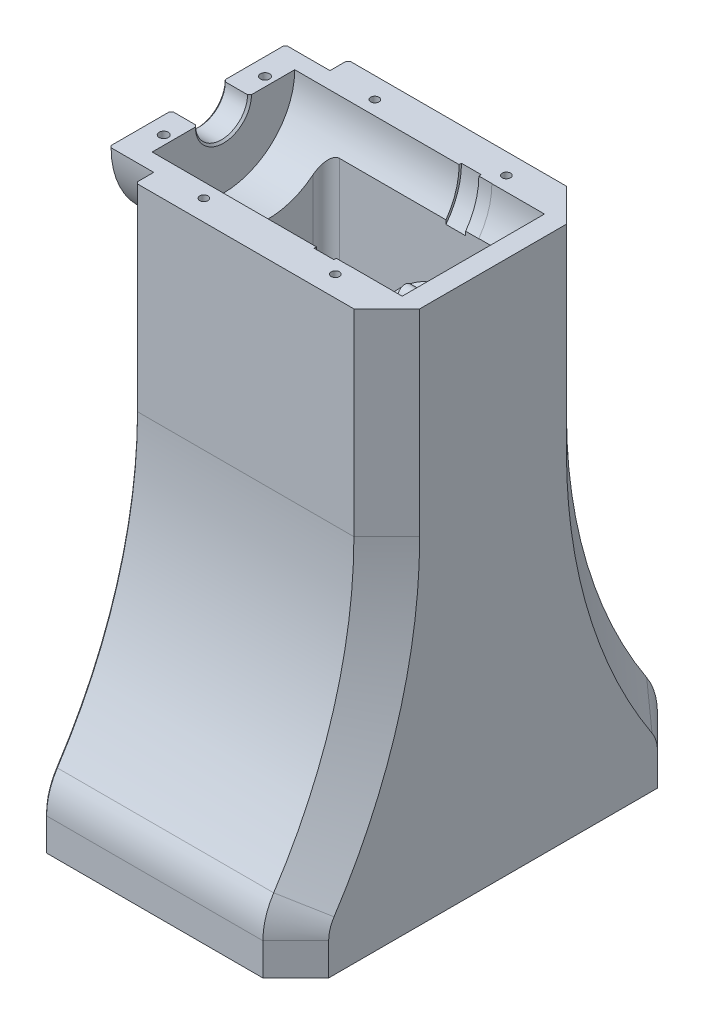
SolidWorks part; units mm, degrees
ref_plane "Front Plane" through (0, 0, 0) normal (0, 0, 1) x (1, 0, 0)
ref_plane "Top Plane" through (0, 0, 0) normal (0, 1, 0) x (1, 0, 0)
ref_plane "Right Plane" through (0, 0, 0) normal (1, 0, 0) x (0, 0, -1)
sketch "Sketch1" plane through (0, 0, 0) normal (0, 0, 1) x (1, 0, 0)
  line L1 (0, 0) -> (0, 5.0292)
  line L2 (0, 5.0292) -> (5.0546, 5.0292)
  line L3 (5.0546, 5.0292) -> (5.0546, 13.7668)
  line L4 (5.0546, 13.7668) -> (36.8046, 13.7668)
  line L5 (43.1546, 13.7668) -> (43.1546, 13.7414)
  line L6 (53.3146, 0) -> (0, 0)
  line L8 (43.1546, 13.7414) -> (53.3146, 13.7414)
  line L9 (53.3146, 13.7414) -> (53.3146, 0)
  line L10 (36.8046, 13.7668) -> (36.8046, 14.224)
  line L11 (36.8046, 14.224) -> (40.6146, 14.224)
  line L12 (40.6146, 14.224) -> (40.6146, 13.7668)
  line L13 (40.6146, 13.7668) -> (43.1546, 13.7668)
  point P8 (38.7096, 14.224)
  dimension "D1" = 5.0546
  dimension "D2" = 31.75
  dimension "D3" = 5.0292
  dimension "D4" = 38.1
  dimension "D5" = 13.7668
  dimension "D6" = 0.0254
  dimension "D7" = 10.16
  dimension "D8" = 35.56
  dimension "D9" = 14.224
revolve "REVOLVE MOTOR" add sketch "Sketch1" angle 360 about L6
sketch "Sketch2" plane through (5.0546, 0, 0) normal (-1, 0, 0) x (0, 0, 1)
  line L0 (0, -14.6304) -> (0, -12.9032) construction
  line L1 (-1.4224, -14.6304) -> (-1.4224, -12.9032)
  line L2 (1.4224, -14.6304) -> (1.4224, -12.9032)
  line L3 (0, 14.6304) -> (0, 12.9032) construction
  line L4 (1.4224, 14.6304) -> (1.4224, 12.9032)
  line L5 (-1.4224, 14.6304) -> (-1.4224, 12.9032)
  arc A0 (-1.4224, -14.6304) -> (1.4224, -14.6304) centre (0, -14.6304) ccw
  arc A1 (1.4224, -12.9032) -> (-1.4224, -12.9032) centre (0, -12.9032) ccw
  arc A2 (1.4224, 14.6304) -> (-1.4224, 14.6304) centre (0, 14.6304) ccw
  arc A3 (-1.4224, 12.9032) -> (1.4224, 12.9032) centre (0, 12.9032) ccw
  circle A4 centre (0, 0) radius 13.7668 construction
  point P3 (0, -13.7668)
  point P8 (0, 13.7668)
  dimension "D1" = 1.4224
  dimension "D2" = 2.286
extrude "TRIM MOTOR" cut sketch "Sketch2" against normal through all from offset 35.052 offset against normal yes
sketch "Sketch3" plane through (0, 0, 0) normal (1, 0, 0) x (0, 0, -1)
  line L0 (0, -103.124) -> (38.1, -103.124)
  line L2 (0, 20.5232) -> (0, -103.124)
  line L3 (20.5232, 0) -> (20.5232, -38.1)
  line L4 (38.1, -96.8921) -> (38.1, -103.124)
  arc A0 (20.5232, 0) -> (0, 20.5232) centre (0, 0) ccw
  arc A2 (20.5232, -38.1) -> (36.016, -89.9214) centre (114.9375, -38.1) ccw
  arc A3 (36.016, -89.9214) -> (38.1, -96.8921) centre (25.4, -96.8921) cw
  point P15 (38.1, -92.964)
  dimension "D3" = 41.0464
  dimension "D7" = 12.7
  dimension "D1" = 103.124
  dimension "D2" = 38.1
  dimension "D5" = 38.1
  dimension "D6" = 10.16
extrude "HOUSING" add sketch "Sketch3" along normal offset from surface (48.514 mm away) 3.81 from offset 8.6106 separate body up to face at (53.3146, 0, 0) offset beyond the face yes
sketch "Sketch4" plane through (8.6106, 0, 0) normal (-1, 0, 0) x (0, 0, 1)
  circle A0 centre (0, 0) radius 17.018
  dimension "D1" = 34.036
extrude "HOUSING FRONT BOSS" add sketch "Sketch4" along normal up to surface (8.6106 mm away) up to plane "Right Plane"
combine bodies "SUBTRACT MOTOR" operation type subtract main body 108 bodies to subtract 106
chamfer "Chamfer1" distance 6.35 angle 45 5 edges at (57.1246, -100.008, -38.1) (57.1246, -93.2543, -37.5679) (57.1246, -65.1439, -24.4793) (57.1246, -19.05, -20.5232) (57.1246, 14.5121, -14.5121)
sketch "Sketch9" plane through (0, 0, 0) normal (0, 1, 0) x (1, 0, 0)
  line L0 (3.302, 9.779) -> (3.302, -9.779) construction
  line L1 (0, 17.018) -> (0, -17.018) construction
  circle A0 centre (3.302, 9.779) radius 0.889
  circle A1 centre (3.302, -9.779) radius 0.889
  point P4 (3.302, 0)
  dimension "D2" = 1.778
  dimension "D1" = 19.558
  dimension "D3" = 3.302
extrude "PINS" cut sketch "Sketch9" against normal through all both and the other way through all
chamfer "Chamfer2" distance 0.381 angle 45 8 edges at (8.6106, -100.008, -38.1) (8.6106, -93.2543, -37.5679) (8.6106, -65.1439, -24.4793) (8.6106, -19.05, -20.5232) (8.6106, 14.5121, -14.5121) (0, 0, -17.018) (0, 0, -5.0292) (5.0546, 0, -5.0292)
split "Split1" trim tools "Top Plane" bodies to split 117 resulting bodies 110 111
sketch "Sketch5" plane through (0, 0, 0) normal (0, 1, 0) x (1, 0, 0)
  line L0 (8.6106, 209.3518) -> (8.6106, 20.5232) construction
  line L1 (13.6906, 0) -> (37.5666, 0)
  line L2 (13.6906, 0) -> (13.6906, 8.6868)
  line L3 (16.2306, 11.2268) -> (35.0266, 11.2268)
  line L4 (37.5666, 0) -> (37.5666, 8.6868)
  line L5 (40.1066, 1.4224) -> (40.1066, 0) construction
  line L7 (5.0546, 13.7668) -> (36.8046, 13.7668) construction
  arc A0 (35.0266, 11.2268) -> (37.5666, 8.6868) centre (35.0266, 8.6868) cw
  arc A1 (13.6906, 8.6868) -> (16.2306, 11.2268) centre (16.2306, 8.6868) cw
  dimension "D3" = 2.54
  dimension "D1" = 5.08
  dimension "D2" = 2.54
  dimension "D4" = 2.54
extrude "Cut-Extrude2" cut sketch "Sketch5" against normal through all
sketch "Sketch7" plane through (0, 0, 0) normal (0, 1, 0) x (1, 0, 0)
  line L0 (13.6906, 0) -> (37.5666, 0) construction
  line L1 (35.0266, 11.2268) -> (49.5046, 11.2268)
  line L2 (35.0266, 11.2268) -> (35.0266, 0)
  line L3 (35.0266, 0) -> (52.0446, 0)
  line L4 (52.0446, 8.6868) -> (52.0446, 0)
  line L5 (57.1246, 14.1732) -> (57.1246, 0) construction
  arc A0 (49.5046, 11.2268) -> (52.0446, 8.6868) centre (49.5046, 8.6868) cw
  arc A1 (16.2306, 11.2268) -> (13.6906, 8.6868) centre (16.2306, 8.6868) ccw construction
  dimension "D1" = 5.08
extrude "Cut-Extrude4" cut sketch "Sketch7" against normal through all from offset 30.48 offset against normal yes
sketch "Sketch6" plane through (0, 0, 0) normal (0, 1, 0) x (1, 0, 0)
  line L0 (53.3146, 13.7414) -> (53.3146, 0) construction
  line L1 (35.0266, 11.2268) -> (50.7746, 11.2268)
  line L2 (35.0266, 11.2268) -> (35.0266, 4.8768)
  line L3 (35.0266, 4.8768) -> (50.7746, 4.8768)
  line L4 (53.3146, 8.6868) -> (53.3146, 7.4168)
  arc A0 (50.7746, 11.2268) -> (53.3146, 8.6868) centre (50.7746, 8.6868) cw
  arc A1 (50.7746, 4.8768) -> (53.3146, 7.4168) centre (50.7746, 7.4168) ccw
  point P9 (53.3146, 11.2268)
  point P12 (53.3146, 4.8768)
  dimension "D2" = 2.54
  dimension "D1" = 6.35
extrude "Cut-Extrude3" cut sketch "Sketch6" against normal blind 22.86
fillet "Fillet2" radius 3.81 1 edges at (37.5666, -18.1109, -4.8768)
hole_wizard "M5x0.8 Tapped Hole1" positions "Sketch10" profile "Sketch12" tap size "M5x0.8" standard "ANSI Metric"
sketch "Sketch10" plane through (0, -103.124, 0) normal (0, -1, 0) x (-1, 0, 0)
  line L0 (-57.1246, 0) -> (-57.1246, 31.75) construction
  line L1 (-8.6106, 0) -> (-8.6106, 37.719) construction
  point P0 (-17.7546, 30.48)
  point P2 (-49.5046, 30.48)
  dimension "D1" = 31.75
  dimension "D2" = 7.62
  dimension "D3" = 30.48
  dimension "D4" = 9.144
  dimension "D5" = 40.894
sketch "Sketch12" plane through (17.7546, -103.124, -30.48) normal (1, 0, 0) x (0, 0, -1)
  line L0 (0, 0) -> (0, 16.2478)
  line L1 (0, 16.2478) -> (2.1, 14.986)
  line L2 (2.1, 14.986) -> (2.1, 0)
  line L5 (2.1, 0) -> (0, 0)
  line L10 (0, 16.2478) -> (-2.1, 14.986) construction
  line L11 (0, -6.35) -> (0, 107.95) construction
  dimension "Tap Drill Dia." = 4.2
  dimension "Tap Drill Depth" = 14.986
  dimension "Drill Angle" = 118
cosmetic thread "Hole Thread1" parameters "D1"=12.7, "D2"=5
cosmetic thread "Hole Thread2" parameters "D1"=12.7, "D2"=5
sketch "Sketch13" plane through (0, 0, 0) normal (0, 1, 0) x (1, 0, 0)
  circle A0 centre (17.78, 16.51) radius 2.54
  circle A1 centre (43.18, 16.51) radius 2.54
  point P5 (0, 0)
  dimension "D1" = 5.08
  dimension "D4" = 25.4
  dimension "D2" = 16.51
  dimension "D3" = 17.78
extrude "C'BORES" cut sketch "Sketch13" along normal through all from offset 4.572
hole_wizard "M2 Clearance Hole1" positions "Sketch14" profile "Sketch15" hole size "M2" standard "ANSI Metric" end condition through all
sketch "Sketch14" plane through (0, 4.572, 0) normal (0, 1, 0) x (1, 0, 0)
  point P0 (17.78, 16.51)
  point P3 (43.18, 16.51)
sketch "Sketch15" plane through (17.78, 4.572, -16.51) normal (1, 0, 0) x (0, 0, 1)
  line L0 (0, 0) -> (0, 107.696)
  line L1 (0, 107.696) -> (1.1, 107.696)
  line L2 (1.1, 107.696) -> (1.1, 0)
  line L5 (1.1, 0) -> (0, 0)
  line L11 (0, -6.35) -> (0, 107.95) construction
  dimension "Thru Hole Dia." = 2.2
  dimension "Thru Hole Depth" = 107.696
hole_wizard "M2x0.4 Tapped Hole1" positions "Sketch16" profile "Sketch17" tap size "M2x0.4" standard "ANSI Metric"
sketch "Sketch16" plane through (0, 0, 0) normal (0, 1, 0) x (1, 0, 0)
  point P0 (17.78, 16.51)
  point P3 (43.18, 16.51)
sketch "Sketch17" plane through (17.78, 0, -16.51) normal (1, 0, 0) x (0, 0, 1)
  line L0 (0, 0) -> (0, 14.4507)
  line L1 (0, 14.4507) -> (0.8, 13.97)
  line L2 (0.8, 13.97) -> (0.8, 0)
  line L5 (0.8, 0) -> (0, 0)
  line L10 (0, 14.4507) -> (-0.8, 13.97) construction
  line L11 (0, -6.35) -> (0, 107.95) construction
  dimension "Tap Drill Dia." = 1.6
  dimension "Tap Drill Depth" = 13.97
  dimension "Drill Angle" = 118
cosmetic thread "Hole Thread3" parameters "D1"=12.7, "D2"=2
cosmetic thread "Hole Thread7" parameters "D1"=12.7, "D2"=2
sketch "Sketch18" plane through (0, 0, -11.2268) normal (0, 0, 1) x (1, 0, 0)
  line L0 (49.5046, -103.124) -> (16.2306, -103.124) construction
  line L1 (25.7556, -54.864) -> (39.9796, -54.864)
  line L2 (25.7556, -54.864) -> (25.7556, -91.694)
  line L3 (25.7556, -91.694) -> (27.5336, -91.694)
  line L4 (39.9796, -54.864) -> (39.9796, -91.694)
  line L6 (27.5336, -91.694) -> (27.5336, -103.124)
  line L7 (27.5336, -103.124) -> (38.2016, -103.124)
  line L8 (38.2016, -91.694) -> (38.2016, -103.124)
  line L9 (38.2016, -91.694) -> (39.9796, -91.694)
  point P10 (32.8676, -103.124)
  dimension "D1" = 14.224
  dimension "D2" = 10.668
  dimension "D3" = 11.43
  dimension "D4" = 48.26
extrude "Cut-Extrude5" cut sketch "Sketch18" against normal blind 10.16
chamfer "Chamfer3" distance 8.89 angle 30 1 edges at (32.8676, -54.864, -21.3868)
ref_plane "Plane1" through (25.7556, -91.694, -11.2268) normal (0, -1, 0) x (-1, 0, 0)
fillet "Fillet3" radius 2.54 5 edges at (38.2016, -97.409, -21.3868) (27.5336, -97.409, -21.3868) (32.8676, -54.864, -11.2268) (32.8676, -54.864, -16.2542) (32.8676, -63.754, -21.3868)
mirror "Mirror1" about plane through (0, 0, 0) normal (0, 0, 1) of bodies 122 120 111 110
cosmetic thread "Hole Thread4" parameters "D1"=12.7, "D2"=2
cosmetic thread "Hole Thread5" parameters "D1"=12.7, "D2"=5
cosmetic thread "Hole Thread6" parameters "D1"=12.7, "D2"=5
cosmetic thread "Hole Thread8" parameters "D1"=12.7, "D2"=2
delete or keep bodies "Body-Delete/Keep 1" type keep bodies bodies 112
